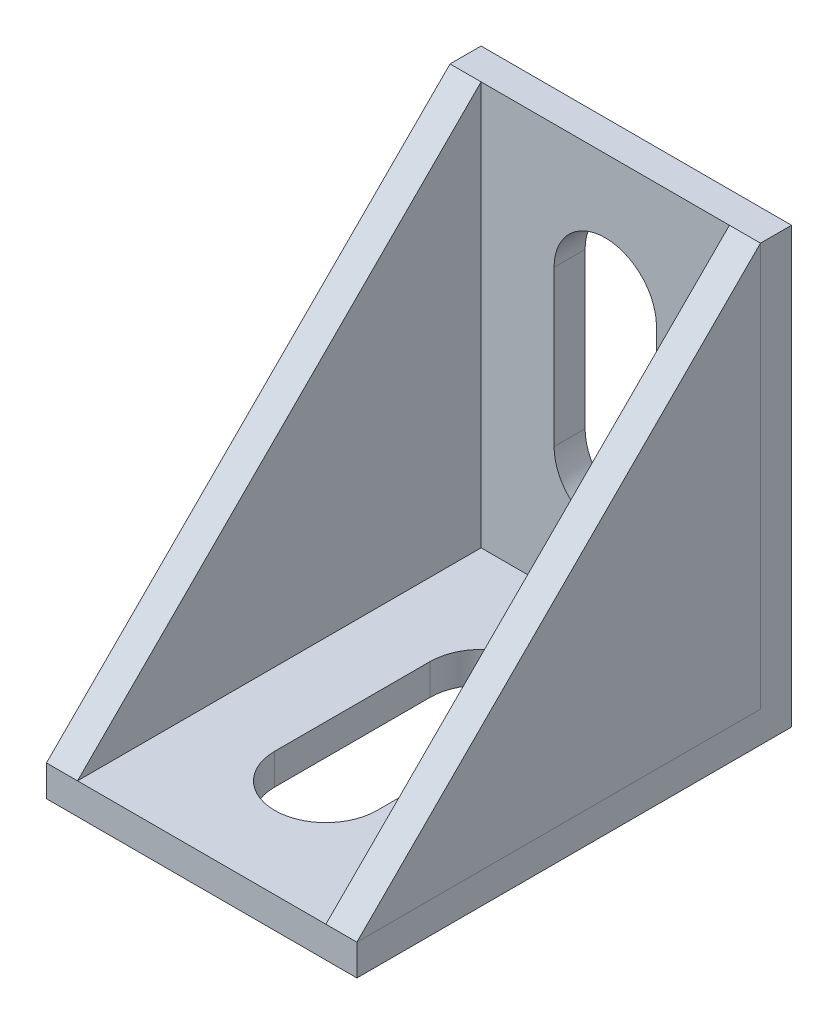
SolidWorks part; units mm, degrees
material "201.0-T43 绝缘成型铸件 (SS)"
ref_plane "前视基准面" through (0, 0, 0) normal (0, 0, 1) x (1, 0, 0)
ref_plane "上视基准面" through (0, 0, 0) normal (0, 1, 0) x (1, 0, 0)
ref_plane "右视基准面" through (0, 0, 0) normal (1, 0, 0) x (0, 0, -1)
sketch "草图3" plane through (0, 0, 0) normal (1, 0, 0) x (0, 0, -1)
  line L0 (4.4622, 21.0807) -> (4.4622, -6.9193)
  line L1 (4.4622, -6.9193) -> (-23.5378, -6.9193)
  line L2 (-23.5378, -6.9193) -> (-23.5378, -4.9193)
  line L3 (4.4622, 21.0807) -> (2.4622, 21.0807)
  line L4 (2.4622, 21.0807) -> (2.4622, -4.9193)
  line L5 (2.4622, -4.9193) -> (-23.5378, -4.9193)
extrude "凸台-拉伸1" add sketch "草图3" along normal blind 20
other "角撑板2" parameters "D1"=2, "D2"=2, "D3"=0, "D4"=0, "D10"=5, "D11"=26, "D12"=26, "D13"=15, "D14"=45, "D15"=15
sketch "草图5" plane through (20, -4.9193, -2.4622) normal (-1, 0, 0) x (0, 0, 1)
  line L0 (0, 0) -> (0, 26)
  line L1 (0, 0) -> (26, 0)
  line L2 (0, 26) -> (26, 0)
other "角撑板3" parameters "D1"=2, "D2"=2, "D3"=0, "D4"=0, "D10"=5, "D11"=26, "D12"=26, "D13"=15, "D14"=45, "D15"=15
sketch "草图6" plane through (0, -4.9193, -2.4622) normal (1, 0, 0) x (0, 0, -1)
  line L0 (0, 0) -> (-26, 0)
  line L1 (0, 0) -> (0, 26)
  line L2 (-26, 0) -> (0, 26)
sketch "草图7" plane through (0, -4.9193, 0) normal (0, 1, 0) x (1, 0, 0)
  line L0 (6.7, -15.5378) -> (6.7, -5.5378)
  line L1 (13.3, -15.5378) -> (13.3, -5.5378)
  arc A0 (13.3, -5.5378) -> (6.7, -5.5378) centre (10, -5.5378) ccw
  arc A1 (13.3, -15.5378) -> (6.7, -15.5378) centre (10, -15.5378) cw
sketch "草图8" plane through (0, 0, -2.4622) normal (0, 0, 1) x (1, 0, 0)
  line L4 (6.7, 3.0807) -> (6.7, 13.0807)
  line L5 (13.3, 3.0807) -> (13.3, 13.0807)
  arc A0 (13.3, 13.0807) -> (6.7, 13.0807) centre (10, 13.0807) ccw
  arc A1 (13.3, 3.0807) -> (6.7, 3.0807) centre (10, 3.0807) cw
extrude "切除-拉伸1" cut sketch "草图7" against normal blind 7 and the other way blind 6
extrude "切除-拉伸2" cut sketch "草图8" against normal blind 3 and the other way blind 5
